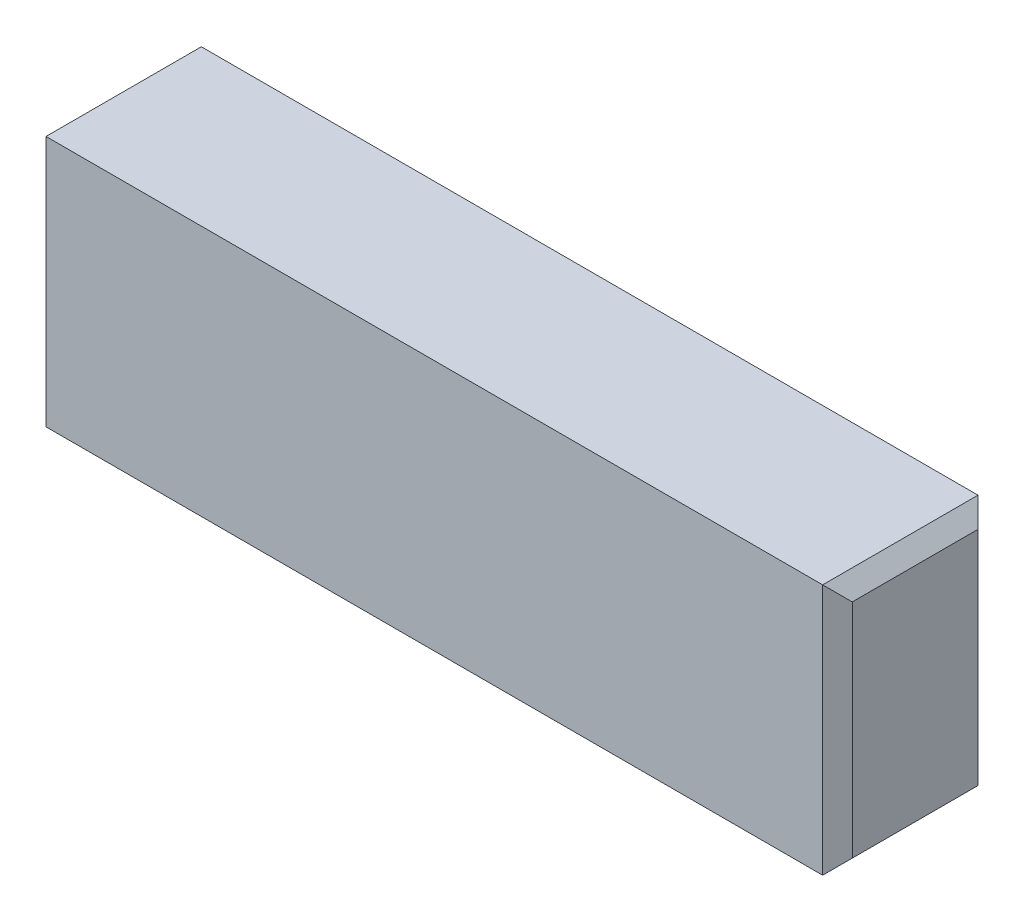
SolidWorks part; units mm, degrees
ref_plane "Front" through (0, 0, 0) normal (0, 0, 1) x (1, 0, 0)
ref_plane "Top" through (0, 0, 0) normal (0, 1, 0) x (1, 0, 0)
ref_plane "Right" through (0, 0, 0) normal (1, 0, 0) x (0, 0, -1)
sketch "Sketch1" plane through (0, 0, 0) normal (0, 0, 1) x (1, 0, 0)
  line L1 (-54.5, 17) -> (54.5, 17)
  line L2 (-54.5, 17) -> (-54.5, -17)
  line L3 (-54.5, -17) -> (54.5, -17)
  line L4 (54.5, 17) -> (54.5, -17)
  line L5 (-54.5, 17) -> (54.5, -17) construction
  line L6 (-54.5, -17) -> (54.5, 17) construction
  point P0 (0, 0)
  dimension "D1" = 109
  dimension "D2" = 34
extrude "Boss-Extrude1" add sketch "Sketch1" along normal blind 21
chamfer "Chamfer1" distance 2 angle 45 8 edges at (-54.5, 17, 10.5) (-54.5, 0, 21) (-54.5, -17, 10.5) (-54.5, 0, 0) (54.5, -17, 10.5) (54.5, 0, 21) (54.5, 17, 10.5) (54.5, 0, 0)
ref_plane "Plane1" through (0, -17, 0) normal (0, -1, 0) x (-1, 0, 0)
sketch "Sketch5" plane through (0, -17, 0) normal (0, -1, 0) x (-1, 0, 0)
  line L0 (0, -21) -> (0, 0) construction
  line L1 (52.5, -21) -> (-52.5, -21) construction
  line L2 (52.5, 0) -> (-52.5, 0) construction
